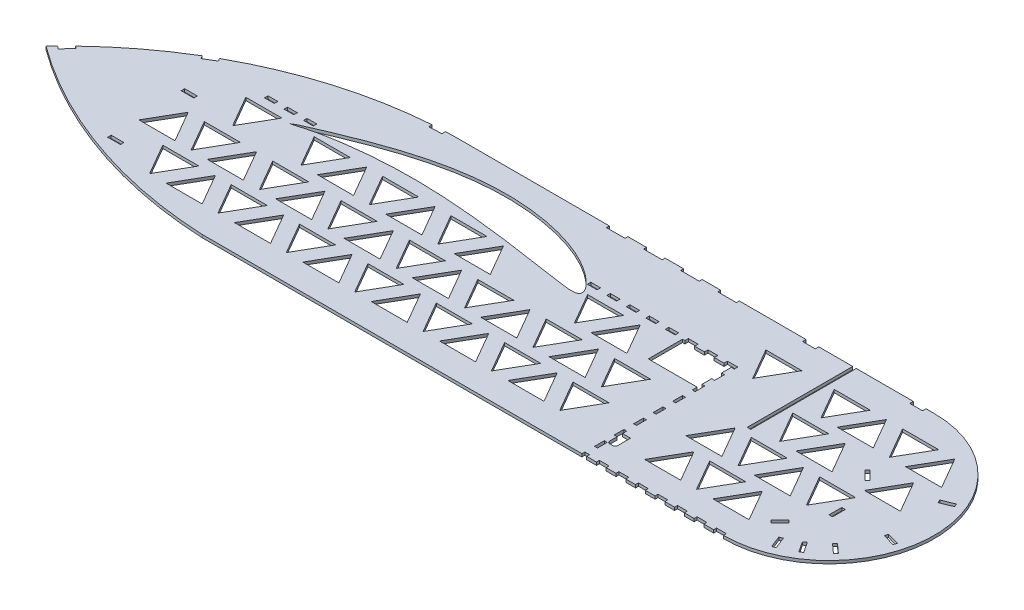
SolidWorks part; units mm, degrees
ref_plane "Front Plane" through (0, 0, 0) normal (0, 0, 1) x (1, 0, 0)
ref_plane "Top Plane" through (0, 0, 0) normal (0, 1, 0) x (1, 0, 0)
ref_plane "Right Plane" through (0, 0, 0) normal (1, 0, 0) x (0, 0, -1)
sketch "Sketch1" plane through (0, 0, 0) normal (0, 1, 0) x (1, 0, 0)
  line L0 (800, 108) -> (0, 108) construction
  line L1 (266.4083, 0) -> (800, 0)
  line L2 (0, 0) -> (0, 216) construction
  line L3 (316.2946, 216) -> (800, 216)
  arc A0 (800, 216) -> (800, 0) centre (800, 108) cw
  arc A2 (266.4083, 0) -> (19.4291, 86.8932) centre (286.1808, 450.645) cw
  arc A4 (19.4291, 86.8932) -> (316.2946, 216) centre (316.2946, -189.8565) cw
  dimension "D1" = 800
  dimension "D2" = 216
extrude "Boss-Extrude1" add sketch "Sketch1" along normal blind 3
sketch "Sketch2" plane through (0, 0, 0) normal (0, -1, 0) x (1, 0, 0)
  line L0 (605.07, -153) -> (605.07, 81) construction
  line L1 (647.57, -153) -> (637.57, -153)
  line L2 (655.07, -153) -> (655.07, -143)
  line L3 (655.07, -118) -> (605.07, -118)
  line L4 (823.6893, -121.2328) -> (814.4969, -130.4252)
  line L5 (814.4969, -130.4252) -> (817.0425, -132.9707)
  line L6 (817.0425, -132.9707) -> (826.2349, -123.7784)
  line L7 (826.2349, -123.7784) -> (823.6893, -121.2328)
  line L8 (823.6893, -121.2328) -> (814.4969, -130.4252)
  line L9 (814.4969, -130.4252) -> (817.0425, -132.9707)
  line L10 (817.0425, -132.9707) -> (826.2349, -123.7784)
  line L11 (826.2349, -123.7784) -> (823.6893, -121.2328)
  line L12 (605.07, -153) -> (605.07, -118)
  line L13 (778.5, -216) -> (791.5, -216) construction
  line L14 (791.5, -216) -> (791.5, -212.4) construction
  line L15 (791.5, -212.4) -> (778.5, -212.4) construction
  line L16 (778.5, -212.4) -> (778.5, -216) construction
  line L17 (668.6076, -216) -> (681.6076, -216) construction
  line L18 (681.6076, -216) -> (681.6076, -212.4) construction
  line L19 (681.6076, -212.4) -> (668.6076, -212.4) construction
  line L20 (833.2163, -28.1278) -> (837.9573, -16.0231)
  line L21 (837.9573, -16.0231) -> (834.6052, -14.7102)
  line L22 (834.6052, -14.7102) -> (829.8642, -26.8149)
  line L23 (829.8642, -26.8149) -> (833.2163, -28.1278)
  line L24 (833.2163, -28.1278) -> (837.9573, -16.0231)
  line L25 (837.9573, -16.0231) -> (834.6052, -14.7102)
  line L26 (834.6052, -14.7102) -> (829.8642, -26.8149)
  line L27 (829.8642, -26.8149) -> (833.2163, -28.1278)
  line L28 (839.4566, -85.3169) -> (839.4566, -72.3169)
  line L29 (839.4566, -72.3169) -> (835.8566, -72.3169)
  line L30 (835.8566, -72.3169) -> (835.8566, -85.3169)
  line L31 (835.8566, -85.3169) -> (839.4566, -85.3169)
  line L32 (839.4566, -85.3169) -> (839.4566, -72.3169)
  line L33 (839.4566, -72.3169) -> (835.8566, -72.3169)
  line L34 (835.8566, -72.3169) -> (835.8566, -85.3169)
  line L35 (835.8566, -85.3169) -> (839.4566, -85.3169)
  line L36 (668.6076, -212.4) -> (668.6076, -216) construction
  line L39 (600.2018, -213) -> (581.2018, -213) construction
  line L40 (658.07, -25.4734) -> (658.07, -38.6734)
  line L41 (663.77, -22.9734) -> (660.57, -22.9734)
  line L42 (666.27, -38.6734) -> (666.27, -25.4734)
  line L43 (658.07, -38.6734) -> (666.27, -38.6734)
  line L44 (658.07, -25.4734) -> (658.07, -33)
  line L45 (663.77, -22.9734) -> (660.57, -22.9734)
  line L46 (666.27, -38.6734) -> (666.27, -25.4734)
  line L47 (658.07, -38.6734) -> (666.27, -38.6734)
  line L48 (581.2018, -213) -> (581.2018, -216) construction
  line L49 (581.2018, -216) -> (600.2018, -216) construction
  line L50 (600.2018, -216) -> (600.2018, -213) construction
  line L51 (562.2018, -213) -> (543.2018, -213) construction
  line L52 (543.2018, -213) -> (543.2018, -216) construction
  line L53 (543.2018, -216) -> (562.2018, -216) construction
  line L54 (562.2018, -216) -> (562.2018, -213) construction
  line L55 (524.2018, -213) -> (505.2018, -213) construction
  line L56 (505.2018, -213) -> (505.2018, -216) construction
  line L57 (505.2018, -216) -> (524.2018, -216) construction
  line L58 (524.2018, -216) -> (524.2018, -213) construction
  line L59 (486.2018, -213) -> (467.2018, -213) construction
  line L60 (467.2018, -213) -> (467.2018, -216) construction
  line L61 (467.2018, -216) -> (486.2018, -216) construction
  line L62 (486.2018, -216) -> (486.2018, -213) construction
  line L63 (286.6536, -215.0679) -> (299.64, -215.6627) construction
  line L64 (299.64, -215.6627) -> (299.8047, -212.0664) construction
  line L65 (299.8047, -212.0664) -> (286.8183, -211.4717) construction
  line L66 (286.8183, -211.4717) -> (286.6536, -215.0679) construction
  line L67 (107.8918, -158.4076) -> (119.0512, -165.0761) construction
  line L68 (119.0512, -165.0761) -> (120.8979, -161.9858) construction
  line L69 (120.8979, -161.9858) -> (109.7385, -155.3173) construction
  line L70 (109.7385, -155.3173) -> (107.8918, -158.4076) construction
  line L71 (25.2251, -93.1105) -> (34.0897, -102.6194) construction
  line L72 (34.0897, -102.6194) -> (36.7229, -100.1646) construction
  line L73 (36.7229, -100.1646) -> (27.8584, -90.6557) construction
  line L74 (27.8584, -90.6557) -> (25.2251, -93.1105) construction
  line L76 (141.0425, -116.6591) -> (128.0425, -116.6591) construction
  line L77 (128.0425, -116.6591) -> (128.0425, -120.2591) construction
  line L79 (212.57, -142.8618) -> (212.57, -142.8948)
  line L80 (128.0425, -120.2591) -> (141.0425, -120.2591) construction
  line L81 (141.0425, -120.2591) -> (141.0425, -116.6591) construction
  line L82 (144.694, -37.8042) -> (131.694, -37.8042) construction
  line L83 (131.694, -37.8042) -> (131.694, -41.4042) construction
  line L84 (131.694, -41.4042) -> (144.694, -41.4042) construction
  line L85 (144.694, -41.4042) -> (144.694, -37.8042) construction
  line L99 (141.0425, -116.6591) -> (128.0425, -116.6591)
  line L101 (128.0425, -116.6591) -> (128.0425, -120.2591)
  line L102 (128.0425, -120.2591) -> (141.0425, -120.2591)
  line L104 (141.0425, -120.2591) -> (141.0425, -116.6591)
  line L105 (144.694, -37.8042) -> (131.694, -37.8042)
  line L106 (131.694, -37.8042) -> (131.694, -41.4042)
  line L108 (131.694, -41.4042) -> (144.694, -41.4042)
  line L110 (144.694, -41.4042) -> (144.694, -37.8042)
  line L111 (237.2859, -101.1604) -> (274.2268, -101.1604)
  line L131 (537.57, -153) -> (527.57, -153) construction
  line L132 (527.57, -153) -> (527.57, -156.6) construction
  line L133 (527.57, -156.6) -> (537.57, -156.6) construction
  line L134 (537.57, -156.6) -> (537.57, -153) construction
  line L135 (557.57, -153) -> (547.57, -153) construction
  line L136 (547.57, -153) -> (547.57, -156.6) construction
  line L137 (547.57, -156.6) -> (557.57, -156.6) construction
  line L138 (557.57, -156.6) -> (557.57, -153) construction
  line L139 (577.57, -153) -> (567.57, -153) construction
  line L140 (567.57, -153) -> (567.57, -156.6) construction
  line L141 (567.57, -156.6) -> (577.57, -156.6) construction
  line L142 (577.57, -156.6) -> (577.57, -153) construction
  line L143 (597.57, -153) -> (587.57, -153) construction
  line L144 (587.57, -153) -> (587.57, -156.6) construction
  line L145 (587.57, -156.6) -> (597.57, -156.6) construction
  line L146 (597.57, -156.6) -> (597.57, -153) construction
  line L148 (607.57, -153) -> (607.57, -156.6) construction
  line L149 (607.57, -156.6) -> (617.57, -156.6) construction
  line L150 (617.57, -156.6) -> (617.57, -153) construction
  line L152 (627.57, -153) -> (627.57, -156.6) construction
  line L153 (627.57, -156.6) -> (637.57, -156.6) construction
  line L154 (637.57, -156.6) -> (637.57, -153) construction
  line L155 (658.07, -153) -> (647.57, -153) construction
  line L156 (647.57, -153) -> (647.57, -156.6) construction
  line L157 (647.57, -156.6) -> (658.07, -156.6) construction
  line L158 (658.07, -156.6) -> (658.07, -153) construction
  line L160 (655.07, -143) -> (658.07, -143) construction
  line L161 (658.07, -143) -> (658.07, -133) construction
  line L162 (658.07, -133) -> (655.07, -133) construction
  line L163 (655.07, -113) -> (655.07, -123) construction
  line L164 (655.07, -123) -> (658.07, -123) construction
  line L165 (658.07, -123) -> (658.07, -113) construction
  line L166 (658.07, -113) -> (655.07, -113) construction
  line L167 (655.07, -93) -> (655.07, -103) construction
  line L168 (655.07, -103) -> (658.07, -103) construction
  line L169 (658.07, -103) -> (658.07, -93) construction
  line L170 (658.07, -93) -> (655.07, -93) construction
  line L171 (655.07, -73) -> (655.07, -83) construction
  line L172 (655.07, -83) -> (658.07, -83) construction
  line L173 (658.07, -83) -> (658.07, -73) construction
  line L174 (658.07, -73) -> (655.07, -73) construction
  line L175 (655.07, -53) -> (655.07, -63) construction
  line L176 (655.07, -63) -> (658.07, -63) construction
  line L177 (658.07, -63) -> (658.07, -53) construction
  line L178 (658.07, -53) -> (655.07, -53) construction
  line L179 (655.07, -33) -> (655.07, -43) construction
  line L180 (655.07, -43) -> (658.07, -43) construction
  line L182 (658.07, -33) -> (655.07, -33) construction
  line L183 (655.07, -13) -> (655.07, -23) construction
  line L184 (655.07, -23) -> (658.07, -23) construction
  line L185 (658.07, -23) -> (658.07, -13) construction
  line L186 (658.07, -13) -> (655.07, -13) construction
  line L187 (660, 0) -> (655.07, 0) construction
  line L188 (879.4661, -142.1765) -> (891.5128, -147.063) construction
  line L189 (891.5128, -147.063) -> (892.866, -143.727) construction
  line L190 (892.866, -143.727) -> (880.8193, -138.8405) construction
  line L191 (880.8193, -138.8405) -> (879.4661, -142.1765) construction
  line L192 (883.5641, -85.6407) -> (896.0497, -82.0199) construction
  line L193 (896.0497, -82.0199) -> (895.047, -78.5624) construction
  line L194 (895.047, -78.5624) -> (882.5614, -82.1832) construction
  line L195 (882.5614, -82.1832) -> (883.5641, -85.6407) construction
  line L196 (865.4007, -51.3816) -> (875.0501, -42.6702) construction
  line L197 (875.0501, -42.6702) -> (872.6378, -39.9981) construction
  line L198 (872.6378, -39.9981) -> (862.9883, -48.7095) construction
  line L199 (862.9883, -48.7095) -> (865.4007, -51.3816) construction
  line L200 (849.1147, -36.7915) -> (856.2715, -25.9389) construction
  line L201 (856.2715, -25.9389) -> (853.2661, -23.957) construction
  line L202 (853.2661, -23.957) -> (846.1093, -34.8096) construction
  line L203 (846.1093, -34.8096) -> (849.1147, -36.7915) construction
  line L204 (822.4089, -44.7346) -> (813.2165, -35.5422) construction
  line L205 (813.2165, -35.5422) -> (810.6709, -38.0878) construction
  line L206 (810.6709, -38.0878) -> (819.8633, -47.2801) construction
  line L207 (819.8633, -47.2801) -> (822.4089, -44.7346) construction
  line L208 (879.4661, -142.1765) -> (891.5128, -147.063)
  line L209 (891.5128, -147.063) -> (892.866, -143.727)
  line L210 (892.866, -143.727) -> (880.8193, -138.8405)
  line L211 (880.8193, -138.8405) -> (879.4661, -142.1765)
  line L212 (883.5641, -85.6407) -> (896.0497, -82.0199)
  line L213 (896.0497, -82.0199) -> (895.047, -78.5624)
  line L214 (895.047, -78.5624) -> (882.5614, -82.1832)
  line L215 (882.5614, -82.1832) -> (883.5641, -85.6407)
  line L216 (865.4007, -51.3816) -> (875.0501, -42.6702)
  line L217 (875.0501, -42.6702) -> (872.6378, -39.9981)
  line L218 (872.6378, -39.9981) -> (862.9883, -48.7095)
  line L219 (862.9883, -48.7095) -> (865.4007, -51.3816)
  line L220 (849.1147, -36.7915) -> (856.2715, -25.9389)
  line L221 (856.2715, -25.9389) -> (853.2661, -23.957)
  line L222 (853.2661, -23.957) -> (846.1093, -34.8096)
  line L223 (846.1093, -34.8096) -> (849.1147, -36.7915)
  line L224 (822.4089, -44.7346) -> (813.2165, -35.5422)
  line L225 (813.2165, -35.5422) -> (810.6709, -38.0878)
  line L226 (810.6709, -38.0878) -> (819.8633, -47.2801)
  line L227 (819.8633, -47.2801) -> (822.4089, -44.7346)
  line L228 (655.07, 0) -> (655.07, -3) construction
  line L229 (655.07, -3) -> (660, -3) construction
  line L230 (660, -3) -> (660, 0) construction
  line L231 (680, 0) -> (670, 0) construction
  line L232 (670, 0) -> (670, -3) construction
  line L233 (670, -3) -> (680, -3) construction
  line L234 (680, -3) -> (680, 0) construction
  line L235 (700, 0) -> (690, 0) construction
  line L236 (690, 0) -> (690, -3) construction
  line L237 (690, -3) -> (700, -3) construction
  line L238 (700, -3) -> (700, 0) construction
  line L239 (720, 0) -> (710, 0) construction
  line L240 (710, 0) -> (710, -3) construction
  line L241 (710, -3) -> (720, -3) construction
  line L242 (720, -3) -> (720, 0) construction
  line L243 (740, 0) -> (730, 0) construction
  line L244 (730, 0) -> (730, -3) construction
  line L245 (730, -3) -> (740, -3) construction
  line L246 (740, -3) -> (740, 0) construction
  line L247 (760, 0) -> (750, 0) construction
  line L248 (750, 0) -> (750, -3) construction
  line L249 (750, -3) -> (760, -3) construction
  line L250 (760, -3) -> (760, 0) construction
  line L251 (780, 0) -> (770, 0) construction
  line L252 (770, 0) -> (770, -3) construction
  line L253 (770, -3) -> (780, -3) construction
  line L254 (780, -3) -> (780, 0) construction
  line L255 (800, 0) -> (790, 0) construction
  line L256 (790, 0) -> (790, -3) construction
  line L257 (790, -3) -> (800, -3) construction
  line L258 (800, -3) -> (800, 0) construction
  line L259 (778.5, -216) -> (791.5, -216)
  line L260 (791.5, -216) -> (791.5, -212.4)
  line L261 (791.5, -212.4) -> (778.5, -212.4)
  line L262 (778.5, -212.4) -> (778.5, -216)
  line L263 (668.6076, -216) -> (681.6076, -216)
  line L264 (681.6076, -216) -> (681.6076, -212.4)
  line L265 (681.6076, -212.4) -> (668.6076, -212.4)
  line L266 (668.6076, -212.4) -> (668.6076, -216)
  line L267 (600.2018, -213) -> (581.2018, -213)
  line L268 (581.2018, -213) -> (581.2018, -216)
  line L269 (581.2018, -216) -> (600.2018, -216)
  line L270 (600.2018, -216) -> (600.2018, -213)
  line L271 (562.2018, -213) -> (543.2018, -213)
  line L272 (543.2018, -213) -> (543.2018, -216)
  line L273 (543.2018, -216) -> (562.2018, -216)
  line L274 (562.2018, -216) -> (562.2018, -213)
  line L275 (524.2018, -213) -> (505.2018, -213)
  line L276 (505.2018, -213) -> (505.2018, -216)
  line L277 (505.2018, -216) -> (524.2018, -216)
  line L278 (524.2018, -216) -> (524.2018, -213)
  line L279 (486.2018, -213) -> (467.2018, -213)
  line L280 (467.2018, -213) -> (467.2018, -216)
  line L281 (467.2018, -216) -> (486.2018, -216)
  line L282 (486.2018, -216) -> (486.2018, -213)
  line L283 (286.6536, -215.0679) -> (299.64, -215.6627)
  line L284 (299.64, -215.6627) -> (299.8047, -212.0664)
  line L285 (299.8047, -212.0664) -> (286.8183, -211.4717)
  line L286 (286.8183, -211.4717) -> (286.6536, -215.0679)
  line L287 (107.8918, -158.4076) -> (119.0512, -165.0761)
  line L288 (119.0512, -165.0761) -> (120.8979, -161.9858)
  line L289 (120.8979, -161.9858) -> (109.7385, -155.3173)
  line L290 (109.7385, -155.3173) -> (107.8918, -158.4076)
  line L291 (25.2251, -93.1105) -> (34.0897, -102.6194)
  line L292 (34.0897, -102.6194) -> (36.7229, -100.1646)
  line L293 (36.7229, -100.1646) -> (27.8584, -90.6557)
  line L294 (27.8584, -90.6557) -> (25.2251, -93.1105)
  line L351 (537.57, -153) -> (527.57, -153)
  line L352 (527.57, -153) -> (527.57, -156.6)
  line L353 (527.57, -156.6) -> (537.57, -156.6)
  line L354 (537.57, -156.6) -> (537.57, -153)
  line L355 (557.57, -153) -> (547.57, -153)
  line L356 (547.57, -153) -> (547.57, -156.6)
  line L357 (547.57, -156.6) -> (557.57, -156.6)
  line L358 (557.57, -156.6) -> (557.57, -153)
  line L359 (577.57, -153) -> (567.57, -153)
  line L360 (567.57, -153) -> (567.57, -156.6)
  line L361 (567.57, -156.6) -> (577.57, -156.6)
  line L362 (577.57, -156.6) -> (577.57, -153)
  line L363 (597.57, -153) -> (587.57, -153)
  line L364 (587.57, -153) -> (587.57, -156.6)
  line L365 (587.57, -156.6) -> (597.57, -156.6)
  line L366 (597.57, -156.6) -> (597.57, -153)
  line L368 (607.57, -153) -> (607.57, -156.6)
  line L369 (607.57, -156.6) -> (617.57, -156.6)
  line L370 (617.57, -156.6) -> (617.57, -153)
  line L372 (627.57, -153) -> (627.57, -156.6)
  line L373 (627.57, -156.6) -> (637.57, -156.6)
  line L374 (637.57, -156.6) -> (637.57, -153)
  line L375 (658.07, -153) -> (655.07, -153)
  line L376 (647.57, -153) -> (647.57, -156.6)
  line L377 (647.57, -156.6) -> (658.07, -156.6)
  line L378 (658.07, -156.6) -> (658.07, -153)
  line L380 (655.07, -143) -> (658.07, -143)
  line L381 (658.07, -143) -> (658.07, -133)
  line L382 (658.07, -133) -> (655.07, -133)
  line L383 (655.07, -113) -> (655.07, -118)
  line L384 (655.07, -123) -> (658.07, -123)
  line L385 (658.07, -123) -> (658.07, -113)
  line L386 (658.07, -113) -> (655.07, -113)
  line L387 (655.07, -93) -> (655.07, -103)
  line L388 (655.07, -103) -> (658.07, -103)
  line L389 (658.07, -103) -> (658.07, -93)
  line L390 (658.07, -93) -> (655.07, -93)
  line L391 (655.07, -73) -> (655.07, -83)
  line L392 (655.07, -83) -> (658.07, -83)
  line L393 (658.07, -83) -> (658.07, -73)
  line L394 (658.07, -73) -> (655.07, -73)
  line L395 (655.07, -53) -> (655.07, -63)
  line L396 (655.07, -63) -> (658.07, -63)
  line L397 (658.07, -63) -> (658.07, -53)
  line L398 (658.07, -53) -> (655.07, -53)
  line L399 (655.07, -33) -> (655.07, -43)
  line L400 (655.07, -43) -> (658.07, -43)
  line L401 (658.07, -43) -> (658.07, -38.6734)
  line L402 (658.07, -33) -> (655.07, -33)
  line L403 (655.07, -13) -> (655.07, -23)
  line L404 (655.07, -23) -> (658.07, -23)
  line L405 (658.07, -23) -> (658.07, -13)
  line L406 (658.07, -13) -> (655.07, -13)
  line L407 (660, 0) -> (655.07, 0)
  line L408 (655.07, 0) -> (655.07, -3)
  line L409 (655.07, -3) -> (660, -3)
  line L410 (660, -3) -> (660, 0)
  line L411 (680, 0) -> (670, 0)
  line L412 (670, 0) -> (670, -3)
  line L413 (670, -3) -> (680, -3)
  line L414 (680, -3) -> (680, 0)
  line L415 (700, 0) -> (690, 0)
  line L416 (690, 0) -> (690, -3)
  line L417 (690, -3) -> (700, -3)
  line L418 (700, -3) -> (700, 0)
  line L419 (720, 0) -> (710, 0)
  line L420 (710, 0) -> (710, -3)
  line L421 (710, -3) -> (720, -3)
  line L422 (720, -3) -> (720, 0)
  line L423 (740, 0) -> (730, 0)
  line L424 (730, 0) -> (730, -3)
  line L425 (730, -3) -> (740, -3)
  line L426 (740, -3) -> (740, 0)
  line L427 (760, 0) -> (750, 0)
  line L428 (750, 0) -> (750, -3)
  line L429 (750, -3) -> (760, -3)
  line L430 (760, -3) -> (760, 0)
  line L431 (780, 0) -> (770, 0)
  line L432 (770, 0) -> (770, -3)
  line L433 (770, -3) -> (780, -3)
  line L434 (780, -3) -> (780, 0)
  line L435 (800, 0) -> (790, 0)
  line L436 (790, 0) -> (790, -3)
  line L437 (790, -3) -> (800, -3)
  line L438 (800, -3) -> (800, 0)
  line L439 (655.07, -133) -> (655.07, -123)
  line L440 (627.57, -153) -> (617.57, -153)
  line L441 (607.57, -153) -> (605.07, -153)
  line L443 (274.2268, -101.1604) -> (255.7563, -69.1686)
  line L444 (255.7563, -69.1686) -> (237.2859, -101.1604)
  line L445 (202.2859, -69.1686) -> (239.2268, -69.1686)
  line L449 (239.2268, -69.1686) -> (220.7563, -101.1604)
  line L450 (220.7563, -101.1604) -> (202.2859, -69.1686)
  line L451 (220.7563, -101.1604) -> (202.2859, -69.1686) construction
  line L452 (239.2268, -69.1686) -> (220.7563, -101.1604) construction
  line L453 (202.2859, -69.1686) -> (239.2268, -69.1686) construction
  line L462 (187.07, -153) -> (177.07, -153) construction
  line L463 (177.07, -153) -> (177.07, -156.6) construction
  line L464 (177.07, -156.6) -> (187.07, -156.6) construction
  line L465 (187.07, -156.6) -> (187.07, -153) construction
  line L466 (207.07, -153) -> (197.07, -153) construction
  line L467 (197.07, -153) -> (197.07, -156.6) construction
  line L468 (197.07, -156.6) -> (207.07, -156.6) construction
  line L469 (207.07, -156.6) -> (207.07, -153) construction
  line L470 (227.07, -153) -> (217.07, -153) construction
  line L471 (217.07, -153) -> (217.07, -156.6) construction
  line L472 (217.07, -156.6) -> (227.07, -156.6) construction
  line L473 (227.07, -156.6) -> (227.07, -153) construction
  line L474 (517.57, -153) -> (507.57, -153) construction
  line L475 (507.57, -153) -> (507.57, -156.6) construction
  line L476 (507.57, -156.6) -> (517.57, -156.6) construction
  line L477 (517.57, -156.6) -> (517.57, -153) construction
  line L478 (187.07, -153) -> (177.07, -153)
  line L479 (177.07, -153) -> (177.07, -156.6)
  line L480 (177.07, -156.6) -> (187.07, -156.6)
  line L481 (187.07, -156.6) -> (187.07, -153)
  line L482 (207.07, -153) -> (197.07, -153)
  line L483 (197.07, -153) -> (197.07, -156.6)
  line L484 (197.07, -156.6) -> (207.07, -156.6)
  line L485 (207.07, -156.6) -> (207.07, -153)
  line L486 (227.07, -153) -> (217.07, -153)
  line L487 (217.07, -153) -> (217.07, -156.6)
  line L488 (217.07, -156.6) -> (227.07, -156.6)
  line L489 (227.07, -156.6) -> (227.07, -153)
  line L490 (517.57, -153) -> (507.57, -153)
  line L491 (507.57, -153) -> (507.57, -156.6)
  line L492 (507.57, -156.6) -> (517.57, -156.6)
  line L493 (517.57, -156.6) -> (517.57, -153)
  line L504 (202.2859, -26.9901) -> (239.2268, -26.9901)
  line L514 (239.2268, -26.9901) -> (220.7563, -58.9818)
  line L515 (132.2859, -69.1686) -> (169.2268, -69.1686)
  line L516 (150.7563, -101.1604) -> (132.2859, -69.1686)
  line L517 (169.2268, -69.1686) -> (150.7563, -101.1604)
  line L518 (202.2859, -69.1686) -> (132.2859, -69.1686) construction
  line L519 (150.7563, -101.1604) -> (220.7563, -101.1604) construction
  line L520 (221.2596, -58.9818) -> (202.7892, -26.9901) construction
  line L521 (167.2859, -101.1604) -> (204.2268, -101.1604)
  line L522 (185.7563, -69.1686) -> (167.2859, -101.1604)
  line L523 (204.2268, -101.1604) -> (185.7563, -69.1686)
  line L524 (239.73, -26.9901) -> (221.2596, -58.9818) construction
  line L525 (202.7892, -26.9901) -> (239.73, -26.9901) construction
  line L526 (132.2859, -26.9901) -> (169.2268, -26.9901) construction
  line L527 (150.7563, -58.9818) -> (132.2859, -26.9901) construction
  line L528 (169.2268, -26.9901) -> (150.7563, -58.9818) construction
  line L529 (166.9552, -58.9818) -> (203.896, -58.9818)
  line L530 (185.4256, -26.9901) -> (166.9552, -58.9818)
  line L531 (203.896, -58.9818) -> (185.4256, -26.9901)
  line L532 (220.7563, -58.9818) -> (202.2859, -26.9901)
  line L533 (236.9552, -58.9818) -> (273.896, -58.9818)
  line L534 (716.4, -108) -> (716.4, -216)
  line L535 (716.4, -216) -> (720, -216)
  line L536 (720, -216) -> (720, -108)
  line L537 (720, -108) -> (716.4, -108)
  line L538 (716.4, -108) -> (716.4, -216)
  line L539 (716.4, -216) -> (720, -216)
  line L540 (720, -216) -> (720, -108)
  line L541 (720, -108) -> (716.4, -108)
  line L542 (273.896, -58.9818) -> (255.4256, -26.9901)
  line L543 (255.4256, -26.9901) -> (236.9552, -58.9818)
  line L544 (307.2859, -101.1604) -> (344.2268, -101.1604)
  line L545 (344.2268, -101.1604) -> (325.7563, -69.1686)
  line L546 (325.7563, -69.1686) -> (307.2859, -101.1604)
  line L547 (272.2859, -69.1686) -> (309.2268, -69.1686)
  line L548 (309.2268, -69.1686) -> (290.7563, -101.1604)
  line L549 (290.7563, -101.1604) -> (272.2859, -69.1686)
  line L550 (272.2859, -26.9901) -> (309.2268, -26.9901)
  line L551 (309.2268, -26.9901) -> (290.7563, -58.9818)
  line L552 (290.7563, -58.9818) -> (272.2859, -26.9901)
  line L553 (306.9552, -58.9818) -> (343.896, -58.9818)
  line L554 (343.896, -58.9818) -> (325.4256, -26.9901)
  line L555 (325.4256, -26.9901) -> (306.9552, -58.9818)
  line L556 (377.2859, -101.1604) -> (414.2268, -101.1604)
  line L557 (414.2268, -101.1604) -> (395.7563, -69.1686)
  line L558 (395.7563, -69.1686) -> (377.2859, -101.1604)
  line L559 (342.2859, -69.1686) -> (379.2268, -69.1686)
  line L560 (379.2268, -69.1686) -> (360.7563, -101.1604)
  line L561 (360.7563, -101.1604) -> (342.2859, -69.1686)
  line L562 (342.2859, -26.9901) -> (379.2268, -26.9901)
  line L563 (379.2268, -26.9901) -> (360.7563, -58.9818)
  line L564 (360.7563, -58.9818) -> (342.2859, -26.9901)
  line L565 (376.9552, -58.9818) -> (413.896, -58.9818)
  line L566 (413.896, -58.9818) -> (395.4256, -26.9901)
  line L567 (395.4256, -26.9901) -> (376.9552, -58.9818)
  line L568 (447.2859, -101.1604) -> (484.2268, -101.1604)
  line L569 (484.2268, -101.1604) -> (465.7563, -69.1686)
  line L570 (465.7563, -69.1686) -> (447.2859, -101.1604)
  line L571 (412.2859, -69.1686) -> (449.2268, -69.1686)
  line L572 (449.2268, -69.1686) -> (430.7563, -101.1604)
  line L573 (430.7563, -101.1604) -> (412.2859, -69.1686)
  line L574 (412.2859, -26.9901) -> (449.2268, -26.9901)
  line L575 (449.2268, -26.9901) -> (430.7563, -58.9818)
  line L576 (430.7563, -58.9818) -> (412.2859, -26.9901)
  line L577 (446.9552, -58.9818) -> (483.896, -58.9818)
  line L578 (483.896, -58.9818) -> (465.4256, -26.9901)
  line L579 (465.4256, -26.9901) -> (446.9552, -58.9818)
  line L580 (517.2859, -101.1604) -> (554.2268, -101.1604)
  line L581 (554.2268, -101.1604) -> (535.7563, -69.1686)
  line L582 (535.7563, -69.1686) -> (517.2859, -101.1604)
  line L583 (482.2859, -69.1686) -> (519.2268, -69.1686)
  line L584 (519.2268, -69.1686) -> (500.7563, -101.1604)
  line L585 (500.7563, -101.1604) -> (482.2859, -69.1686)
  line L586 (482.2859, -26.9901) -> (519.2268, -26.9901)
  line L587 (519.2268, -26.9901) -> (500.7563, -58.9818)
  line L588 (500.7563, -58.9818) -> (482.2859, -26.9901)
  line L589 (516.9552, -58.9818) -> (553.896, -58.9818)
  line L590 (553.896, -58.9818) -> (535.4256, -26.9901)
  line L591 (535.4256, -26.9901) -> (516.9552, -58.9818)
  line L592 (587.2859, -101.1604) -> (624.2268, -101.1604)
  line L593 (624.2268, -101.1604) -> (605.7563, -69.1686)
  line L594 (605.7563, -69.1686) -> (587.2859, -101.1604)
  line L595 (552.2859, -69.1686) -> (589.2268, -69.1686)
  line L596 (589.2268, -69.1686) -> (570.7563, -101.1604)
  line L597 (570.7563, -101.1604) -> (552.2859, -69.1686)
  line L598 (552.2859, -26.9901) -> (589.2268, -26.9901)
  line L599 (589.2268, -26.9901) -> (570.7563, -58.9818)
  line L600 (570.7563, -58.9818) -> (552.2859, -26.9901)
  line L601 (586.9552, -58.9818) -> (623.896, -58.9818)
  line L602 (623.896, -58.9818) -> (605.4256, -26.9901)
  line L603 (605.4256, -26.9901) -> (586.9552, -58.9818)
  line L616 (727.2859, -101.1604) -> (764.2268, -101.1604)
  line L617 (764.2268, -101.1604) -> (745.7563, -69.1686)
  line L618 (745.7563, -69.1686) -> (727.2859, -101.1604)
  line L619 (692.2859, -69.1686) -> (729.2268, -69.1686)
  line L620 (729.2268, -69.1686) -> (710.7563, -101.1604)
  line L621 (710.7563, -101.1604) -> (692.2859, -69.1686)
  line L622 (692.2859, -26.9901) -> (729.2268, -26.9901)
  line L623 (729.2268, -26.9901) -> (710.7563, -58.9818)
  line L624 (710.7563, -58.9818) -> (692.2859, -26.9901)
  line L625 (726.9552, -58.9818) -> (763.896, -58.9818)
  line L626 (763.896, -58.9818) -> (745.4256, -26.9901)
  line L627 (745.4256, -26.9901) -> (726.9552, -58.9818)
  line L628 (797.2859, -101.1604) -> (834.2268, -101.1604)
  line L629 (834.2268, -101.1604) -> (815.7563, -69.1686)
  line L630 (815.7563, -69.1686) -> (797.2859, -101.1604)
  line L631 (762.2859, -69.1686) -> (799.2268, -69.1686)
  line L632 (799.2268, -69.1686) -> (780.7563, -101.1604)
  line L633 (780.7563, -101.1604) -> (762.2859, -69.1686)
  line L634 (762.2859, -26.9901) -> (799.2268, -26.9901)
  line L635 (799.2268, -26.9901) -> (780.7563, -58.9818)
  line L636 (780.7563, -58.9818) -> (762.2859, -26.9901)
  line L661 (236.9552, -143.9818) -> (273.896, -143.9818)
  line L662 (273.896, -143.9818) -> (255.4256, -111.9901)
  line L663 (255.4256, -111.9901) -> (236.9552, -143.9818)
  line L670 (272.2859, -111.9901) -> (309.2268, -111.9901)
  line L671 (309.2268, -111.9901) -> (290.7563, -143.9818)
  line L672 (290.7563, -143.9818) -> (272.2859, -111.9901)
  line L673 (306.9552, -143.9818) -> (343.896, -143.9818)
  line L674 (343.896, -143.9818) -> (325.4256, -111.9901)
  line L675 (325.4256, -111.9901) -> (306.9552, -143.9818)
  line L682 (342.2859, -111.9901) -> (379.2268, -111.9901)
  line L683 (379.2268, -111.9901) -> (360.7563, -143.9818)
  line L684 (360.7563, -143.9818) -> (342.2859, -111.9901)
  line L685 (376.9552, -143.9818) -> (413.896, -143.9818)
  line L686 (413.896, -143.9818) -> (395.4256, -111.9901)
  line L687 (395.4256, -111.9901) -> (376.9552, -143.9818)
  line L694 (412.2859, -111.9901) -> (449.2268, -111.9901)
  line L695 (449.2268, -111.9901) -> (430.7563, -143.9818)
  line L696 (430.7563, -143.9818) -> (412.2859, -111.9901)
  line L709 (516.9552, -143.9818) -> (553.896, -143.9818)
  line L710 (553.896, -143.9818) -> (535.4256, -111.9901)
  line L711 (535.4256, -111.9901) -> (516.9552, -143.9818)
  line L718 (552.2859, -111.9901) -> (589.2268, -111.9901)
  line L719 (589.2268, -111.9901) -> (570.7563, -143.9818)
  line L720 (570.7563, -143.9818) -> (552.2859, -111.9901)
  line L724 (657.2859, -186.1604) -> (694.2268, -186.1604)
  line L725 (694.2268, -186.1604) -> (675.7563, -154.1686)
  line L726 (675.7563, -154.1686) -> (657.2859, -186.1604)
  line L736 (727.2859, -186.1604) -> (764.2268, -186.1604)
  line L737 (764.2268, -186.1604) -> (745.7563, -154.1686)
  line L738 (745.7563, -154.1686) -> (727.2859, -186.1604)
  line L745 (726.9552, -143.9818) -> (763.896, -143.9818)
  line L746 (763.896, -143.9818) -> (745.4256, -111.9901)
  line L747 (745.4256, -111.9901) -> (726.9552, -143.9818)
  line L748 (797.2859, -186.1604) -> (834.2268, -186.1604)
  line L749 (834.2268, -186.1604) -> (815.7563, -154.1686)
  line L750 (815.7563, -154.1686) -> (797.2859, -186.1604)
  line L751 (762.2859, -154.1686) -> (799.2268, -154.1686)
  line L752 (799.2268, -154.1686) -> (780.7563, -186.1604)
  line L753 (780.7563, -186.1604) -> (762.2859, -154.1686)
  line L754 (762.2859, -111.9901) -> (799.2268, -111.9901)
  line L755 (799.2268, -111.9901) -> (780.7563, -143.9818)
  line L756 (780.7563, -143.9818) -> (762.2859, -111.9901)
  line L763 (832.2859, -154.1686) -> (869.2268, -154.1686)
  line L764 (869.2268, -154.1686) -> (850.7563, -186.1604)
  line L765 (850.7563, -186.1604) -> (832.2859, -154.1686)
  line L766 (832.2859, -111.9901) -> (869.2268, -111.9901)
  line L767 (869.2268, -111.9901) -> (850.7563, -143.9818)
  line L768 (850.7563, -143.9818) -> (832.2859, -111.9901)
  line L901 (166.9552, -143.9818) -> (203.896, -143.9818)
  line L902 (203.896, -143.9818) -> (185.4256, -111.9901)
  line L903 (185.4256, -111.9901) -> (166.9552, -143.9818)
  line L916 (167.2859, -101.1604) -> (237.2859, -101.1604) construction
  line L917 (167.2859, -101.1604) -> (167.2859, -186.1604) construction
  line L918 (832.2859, -69.1686) -> (869.2268, -69.1686) [skipped]
  line L919 (869.2268, -69.1686) -> (850.7563, -101.1604) [skipped]
  line L920 (850.7563, -101.1604) -> (832.2859, -69.1686) [skipped]
  line L921 (796.9552, -58.9818) -> (833.896, -58.9818) [skipped]
  line L922 (833.896, -58.9818) -> (815.4256, -26.9901) [skipped]
  line L923 (815.4256, -26.9901) -> (796.9552, -58.9818) [skipped]
  line L924 (796.9552, -143.9818) -> (833.896, -143.9818) [skipped]
  line L925 (833.896, -143.9818) -> (815.4256, -111.9901) [skipped]
  line L926 (815.4256, -111.9901) -> (796.9552, -143.9818) [skipped]
  line L927 (866.9552, -58.9818) -> (903.896, -58.9818) [skipped]
  line L928 (903.896, -58.9818) -> (885.4256, -26.9901) [skipped]
  line L929 (885.4256, -26.9901) -> (866.9552, -58.9818) [skipped]
  line L930 (832.2859, -26.9901) -> (869.2268, -26.9901) [skipped]
  line L931 (869.2268, -26.9901) -> (850.7563, -58.9818) [skipped]
  line L932 (850.7563, -58.9818) -> (832.2859, -26.9901) [skipped]
  line L933 (867.2859, -101.1604) -> (904.2268, -101.1604) [skipped]
  line L934 (904.2268, -101.1604) -> (885.7563, -69.1686) [skipped]
  line L935 (885.7563, -69.1686) -> (867.2859, -101.1604) [skipped]
  line L936 (866.9552, -143.9818) -> (903.896, -143.9818) [skipped]
  line L937 (903.896, -143.9818) -> (885.4256, -111.9901) [skipped]
  line L938 (885.4256, -111.9901) -> (866.9552, -143.9818) [skipped]
  line L939 (867.2859, -186.1604) -> (904.2268, -186.1604) [skipped]
  line L940 (904.2268, -186.1604) -> (885.7563, -154.1686) [skipped]
  line L941 (885.7563, -154.1686) -> (867.2859, -186.1604) [skipped]
  line L942 (832.2859, -196.9901) -> (869.2268, -196.9901) [skipped]
  line L943 (869.2268, -196.9901) -> (850.7563, -228.9818) [skipped]
  line L944 (850.7563, -228.9818) -> (832.2859, -196.9901) [skipped]
  line L945 (796.9552, -228.9818) -> (833.896, -228.9818) [skipped]
  line L946 (833.896, -228.9818) -> (815.4256, -196.9901) [skipped]
  line L947 (815.4256, -196.9901) -> (796.9552, -228.9818) [skipped]
  line L948 (866.9552, -228.9818) -> (903.896, -228.9818) [skipped]
  line L949 (903.896, -228.9818) -> (885.4256, -196.9901) [skipped]
  line L950 (885.4256, -196.9901) -> (866.9552, -228.9818) [skipped]
  line L951 (867.2859, -271.1604) -> (904.2268, -271.1604) [skipped]
  line L952 (904.2268, -271.1604) -> (885.7563, -239.1686) [skipped]
  line L953 (885.7563, -239.1686) -> (867.2859, -271.1604) [skipped]
  line L954 (832.2859, -239.1686) -> (869.2268, -239.1686) [skipped]
  line L955 (869.2268, -239.1686) -> (850.7563, -271.1604) [skipped]
  line L956 (850.7563, -271.1604) -> (832.2859, -239.1686) [skipped]
  line L957 (797.2859, -271.1604) -> (834.2268, -271.1604) [skipped]
  line L958 (834.2268, -271.1604) -> (815.7563, -239.1686) [skipped]
  line L959 (815.7563, -239.1686) -> (797.2859, -271.1604) [skipped]
  line L960 (762.2859, -239.1686) -> (799.2268, -239.1686) [skipped]
  line L961 (799.2268, -239.1686) -> (780.7563, -271.1604) [skipped]
  line L962 (780.7563, -271.1604) -> (762.2859, -239.1686) [skipped]
  line L963 (727.2859, -271.1604) -> (764.2268, -271.1604) [skipped]
  line L964 (764.2268, -271.1604) -> (745.7563, -239.1686) [skipped]
  line L965 (745.7563, -239.1686) -> (727.2859, -271.1604) [skipped]
  line L966 (692.2859, -239.1686) -> (729.2268, -239.1686) [skipped]
  line L967 (729.2268, -239.1686) -> (710.7563, -271.1604) [skipped]
  line L968 (710.7563, -271.1604) -> (692.2859, -239.1686) [skipped]
  line L969 (657.2859, -271.1604) -> (694.2268, -271.1604) [skipped]
  line L970 (694.2268, -271.1604) -> (675.7563, -239.1686) [skipped]
  line L971 (675.7563, -239.1686) -> (657.2859, -271.1604) [skipped]
  line L972 (622.2859, -239.1686) -> (659.2268, -239.1686) [skipped]
  line L973 (659.2268, -239.1686) -> (640.7563, -271.1604) [skipped]
  line L974 (640.7563, -271.1604) -> (622.2859, -239.1686) [skipped]
  line L975 (587.2859, -271.1604) -> (624.2268, -271.1604) [skipped]
  line L976 (624.2268, -271.1604) -> (605.7563, -239.1686) [skipped]
  line L977 (605.7563, -239.1686) -> (587.2859, -271.1604) [skipped]
  line L978 (552.2859, -239.1686) -> (589.2268, -239.1686) [skipped]
  line L979 (589.2268, -239.1686) -> (570.7563, -271.1604) [skipped]
  line L980 (570.7563, -271.1604) -> (552.2859, -239.1686) [skipped]
  line L981 (517.2859, -271.1604) -> (554.2268, -271.1604) [skipped]
  line L982 (554.2268, -271.1604) -> (535.7563, -239.1686) [skipped]
  line L983 (535.7563, -239.1686) -> (517.2859, -271.1604) [skipped]
  line L984 (482.2859, -239.1686) -> (519.2268, -239.1686) [skipped]
  line L985 (519.2268, -239.1686) -> (500.7563, -271.1604) [skipped]
  line L986 (500.7563, -271.1604) -> (482.2859, -239.1686) [skipped]
  line L987 (447.2859, -271.1604) -> (484.2268, -271.1604) [skipped]
  line L988 (484.2268, -271.1604) -> (465.7563, -239.1686) [skipped]
  line L989 (465.7563, -239.1686) -> (447.2859, -271.1604) [skipped]
  line L990 (762.2859, -196.9901) -> (799.2268, -196.9901) [skipped]
  line L991 (799.2268, -196.9901) -> (780.7563, -228.9818) [skipped]
  line L992 (780.7563, -228.9818) -> (762.2859, -196.9901) [skipped]
  line L993 (726.9552, -228.9818) -> (763.896, -228.9818) [skipped]
  line L994 (763.896, -228.9818) -> (745.4256, -196.9901) [skipped]
  line L995 (745.4256, -196.9901) -> (726.9552, -228.9818) [skipped]
  line L996 (692.2859, -196.9901) -> (729.2268, -196.9901) [skipped]
  line L997 (729.2268, -196.9901) -> (710.7563, -228.9818) [skipped]
  line L998 (710.7563, -228.9818) -> (692.2859, -196.9901) [skipped]
  line L999 (656.9552, -228.9818) -> (693.896, -228.9818) [skipped]
  line L1000 (693.896, -228.9818) -> (675.4256, -196.9901) [skipped]
  line L1001 (675.4256, -196.9901) -> (656.9552, -228.9818) [skipped]
  line L1002 (622.2859, -196.9901) -> (659.2268, -196.9901) [skipped]
  line L1003 (659.2268, -196.9901) -> (640.7563, -228.9818) [skipped]
  line L1004 (640.7563, -228.9818) -> (622.2859, -196.9901) [skipped]
  line L1005 (586.9552, -228.9818) -> (623.896, -228.9818) [skipped]
  line L1006 (623.896, -228.9818) -> (605.4256, -196.9901) [skipped]
  line L1007 (605.4256, -196.9901) -> (586.9552, -228.9818) [skipped]
  line L1008 (552.2859, -196.9901) -> (589.2268, -196.9901) [skipped]
  line L1009 (589.2268, -196.9901) -> (570.7563, -228.9818) [skipped]
  line L1010 (570.7563, -228.9818) -> (552.2859, -196.9901) [skipped]
  line L1011 (516.9552, -228.9818) -> (553.896, -228.9818) [skipped]
  line L1012 (553.896, -228.9818) -> (535.4256, -196.9901) [skipped]
  line L1013 (535.4256, -196.9901) -> (516.9552, -228.9818) [skipped]
  line L1014 (482.2859, -196.9901) -> (519.2268, -196.9901) [skipped]
  line L1015 (519.2268, -196.9901) -> (500.7563, -228.9818) [skipped]
  line L1016 (500.7563, -228.9818) -> (482.2859, -196.9901) [skipped]
  line L1017 (692.2859, -154.1686) -> (729.2268, -154.1686) [skipped]
  line L1018 (729.2268, -154.1686) -> (710.7563, -186.1604) [skipped]
  line L1019 (710.7563, -186.1604) -> (692.2859, -154.1686) [skipped]
  line L1020 (692.2859, -111.9901) -> (729.2268, -111.9901) [skipped]
  line L1021 (729.2268, -111.9901) -> (710.7563, -143.9818) [skipped]
  line L1022 (710.7563, -143.9818) -> (692.2859, -111.9901) [skipped]
  line L1023 (622.2859, -154.1686) -> (659.2268, -154.1686) [skipped]
  line L1024 (659.2268, -154.1686) -> (640.7563, -186.1604) [skipped]
  line L1025 (640.7563, -186.1604) -> (622.2859, -154.1686) [skipped]
  line L1026 (622.2859, -111.9901) -> (659.2268, -111.9901) [skipped]
  line L1027 (640.7563, -143.9818) -> (622.2859, -111.9901) [skipped]
  line L1028 (659.2268, -111.9901) -> (640.7563, -143.9818) [skipped]
  line L1029 (622.2859, -69.1686) -> (659.2268, -69.1686) [skipped]
  line L1030 (640.7563, -101.1604) -> (622.2859, -69.1686) [skipped]
  line L1031 (659.2268, -69.1686) -> (640.7563, -101.1604) [skipped]
  line L1032 (622.2859, -26.9901) -> (659.2268, -26.9901) [skipped]
  line L1033 (640.7563, -58.9818) -> (622.2859, -26.9901) [skipped]
  line L1034 (659.2268, -26.9901) -> (640.7563, -58.9818) [skipped]
  line L1035 (675.4256, -26.9901) -> (656.9552, -58.9818) [skipped]
  line L1036 (693.896, -58.9818) -> (675.4256, -26.9901) [skipped]
  line L1037 (656.9552, -58.9818) -> (693.896, -58.9818) [skipped]
  line L1038 (675.7563, -69.1686) -> (657.2859, -101.1604) [skipped]
  line L1039 (694.2268, -101.1604) -> (675.7563, -69.1686) [skipped]
  line L1040 (657.2859, -101.1604) -> (694.2268, -101.1604) [skipped]
  line L1041 (675.4256, -111.9901) -> (656.9552, -143.9818) [skipped]
  line L1042 (693.896, -143.9818) -> (675.4256, -111.9901) [skipped]
  line L1043 (656.9552, -143.9818) -> (693.896, -143.9818) [skipped]
  line L1044 (605.4256, -111.9901) -> (586.9552, -143.9818) [skipped]
  line L1045 (623.896, -143.9818) -> (605.4256, -111.9901) [skipped]
  line L1046 (586.9552, -143.9818) -> (623.896, -143.9818) [skipped]
  line L1047 (482.2859, -154.1686) -> (519.2268, -154.1686) [skipped]
  line L1048 (519.2268, -154.1686) -> (500.7563, -186.1604) [skipped]
  line L1049 (500.7563, -186.1604) -> (482.2859, -154.1686) [skipped]
  line L1050 (517.2859, -186.1604) -> (554.2268, -186.1604) [skipped]
  line L1051 (554.2268, -186.1604) -> (535.7563, -154.1686) [skipped]
  line L1052 (535.7563, -154.1686) -> (517.2859, -186.1604) [skipped]
  line L1053 (552.2859, -154.1686) -> (589.2268, -154.1686) [skipped]
  line L1054 (589.2268, -154.1686) -> (570.7563, -186.1604) [skipped]
  line L1055 (570.7563, -186.1604) -> (552.2859, -154.1686) [skipped]
  line L1056 (587.2859, -186.1604) -> (624.2268, -186.1604) [skipped]
  line L1057 (624.2268, -186.1604) -> (605.7563, -154.1686) [skipped]
  line L1058 (605.7563, -154.1686) -> (587.2859, -186.1604) [skipped]
  line L1059 (484.2268, -186.1604) -> (465.7563, -154.1686) [skipped]
  line L1060 (465.7563, -154.1686) -> (447.2859, -186.1604) [skipped]
  line L1061 (447.2859, -186.1604) -> (484.2268, -186.1604) [skipped]
  line L1062 (412.2859, -154.1686) -> (449.2268, -154.1686) [skipped]
  line L1063 (430.7563, -186.1604) -> (412.2859, -154.1686) [skipped]
  line L1064 (449.2268, -154.1686) -> (430.7563, -186.1604) [skipped]
  line L1065 (395.7563, -154.1686) -> (377.2859, -186.1604) [skipped]
  line L1066 (414.2268, -186.1604) -> (395.7563, -154.1686) [skipped]
  line L1067 (377.2859, -186.1604) -> (414.2268, -186.1604) [skipped]
  line L1068 (379.2268, -154.1686) -> (360.7563, -186.1604) [skipped]
  line L1069 (342.2859, -154.1686) -> (379.2268, -154.1686) [skipped]
  line L1070 (360.7563, -186.1604) -> (342.2859, -154.1686) [skipped]
  line L1071 (325.7563, -154.1686) -> (307.2859, -186.1604) [skipped]
  line L1072 (344.2268, -186.1604) -> (325.7563, -154.1686) [skipped]
  line L1073 (307.2859, -186.1604) -> (344.2268, -186.1604) [skipped]
  line L1074 (309.2268, -154.1686) -> (290.7563, -186.1604) [skipped]
  line L1075 (290.7563, -186.1604) -> (272.2859, -154.1686) [skipped]
  line L1076 (272.2859, -154.1686) -> (309.2268, -154.1686) [skipped]
  line L1077 (274.2268, -186.1604) -> (255.7563, -154.1686) [skipped]
  line L1078 (237.2859, -186.1604) -> (274.2268, -186.1604) [skipped]
  line L1079 (255.7563, -154.1686) -> (237.2859, -186.1604) [skipped]
  line L1080 (220.7563, -186.1604) -> (202.2859, -154.1686) [skipped]
  line L1081 (202.2859, -154.1686) -> (239.2268, -154.1686) [skipped]
  line L1082 (239.2268, -154.1686) -> (220.7563, -186.1604) [skipped]
  line L1083 (220.7563, -228.9818) -> (202.2859, -196.9901) [skipped]
  line L1084 (202.2859, -196.9901) -> (239.2268, -196.9901) [skipped]
  line L1085 (239.2268, -196.9901) -> (220.7563, -228.9818) [skipped]
  line L1086 (220.7563, -271.1604) -> (202.2859, -239.1686) [skipped]
  line L1087 (202.2859, -239.1686) -> (239.2268, -239.1686) [skipped]
  line L1088 (239.2268, -239.1686) -> (220.7563, -271.1604) [skipped]
  line L1089 (237.2859, -271.1604) -> (274.2268, -271.1604) [skipped]
  line L1090 (255.7563, -239.1686) -> (237.2859, -271.1604) [skipped]
  line L1091 (274.2268, -271.1604) -> (255.7563, -239.1686) [skipped]
  line L1092 (236.9552, -228.9818) -> (273.896, -228.9818) [skipped]
  line L1093 (273.896, -228.9818) -> (255.4256, -196.9901) [skipped]
  line L1094 (255.4256, -196.9901) -> (236.9552, -228.9818) [skipped]
  line L1095 (290.7563, -228.9818) -> (272.2859, -196.9901) [skipped]
  line L1096 (309.2268, -196.9901) -> (290.7563, -228.9818) [skipped]
  line L1097 (272.2859, -196.9901) -> (309.2268, -196.9901) [skipped]
  line L1098 (325.4256, -196.9901) -> (306.9552, -228.9818) [skipped]
  line L1099 (306.9552, -228.9818) -> (343.896, -228.9818) [skipped]
  line L1100 (343.896, -228.9818) -> (325.4256, -196.9901) [skipped]
  line L1101 (272.2859, -239.1686) -> (309.2268, -239.1686) [skipped]
  line L1102 (309.2268, -239.1686) -> (290.7563, -271.1604) [skipped]
  line L1103 (290.7563, -271.1604) -> (272.2859, -239.1686) [skipped]
  line L1104 (325.7563, -239.1686) -> (307.2859, -271.1604) [skipped]
  line L1105 (307.2859, -271.1604) -> (344.2268, -271.1604) [skipped]
  line L1106 (344.2268, -271.1604) -> (325.7563, -239.1686) [skipped]
  line L1107 (360.7563, -271.1604) -> (342.2859, -239.1686) [skipped]
  line L1108 (379.2268, -239.1686) -> (360.7563, -271.1604) [skipped]
  line L1109 (342.2859, -239.1686) -> (379.2268, -239.1686) [skipped]
  line L1110 (379.2268, -196.9901) -> (360.7563, -228.9818) [skipped]
  line L1111 (360.7563, -228.9818) -> (342.2859, -196.9901) [skipped]
  line L1112 (342.2859, -196.9901) -> (379.2268, -196.9901) [skipped]
  line L1113 (395.4256, -196.9901) -> (376.9552, -228.9818) [skipped]
  line L1114 (376.9552, -228.9818) -> (413.896, -228.9818) [skipped]
  line L1115 (413.896, -228.9818) -> (395.4256, -196.9901) [skipped]
  line L1116 (414.2268, -271.1604) -> (395.7563, -239.1686) [skipped]
  line L1117 (395.7563, -239.1686) -> (377.2859, -271.1604) [skipped]
  line L1118 (377.2859, -271.1604) -> (414.2268, -271.1604) [skipped]
  line L1119 (430.7563, -271.1604) -> (412.2859, -239.1686) [skipped]
  line L1120 (449.2268, -239.1686) -> (430.7563, -271.1604) [skipped]
  line L1121 (412.2859, -239.1686) -> (449.2268, -239.1686) [skipped]
  line L1122 (430.7563, -228.9818) -> (412.2859, -196.9901) [skipped]
  line L1123 (449.2268, -196.9901) -> (430.7563, -228.9818) [skipped]
  line L1124 (412.2859, -196.9901) -> (449.2268, -196.9901) [skipped]
  line L1125 (465.4256, -196.9901) -> (446.9552, -228.9818) [skipped]
  line L1126 (483.896, -228.9818) -> (465.4256, -196.9901) [skipped]
  line L1127 (446.9552, -228.9818) -> (483.896, -228.9818) [skipped]
  line L1128 (166.9552, -228.9818) -> (203.896, -228.9818) [skipped]
  line L1129 (203.896, -228.9818) -> (185.4256, -196.9901) [skipped]
  line L1130 (185.4256, -196.9901) -> (166.9552, -228.9818) [skipped]
  line L1131 (132.2859, -196.9901) -> (169.2268, -196.9901) [skipped]
  line L1132 (169.2268, -196.9901) -> (150.7563, -228.9818) [skipped]
  line L1133 (150.7563, -228.9818) -> (132.2859, -196.9901) [skipped]
  line L1134 (132.2859, -239.1686) -> (169.2268, -239.1686) [skipped]
  line L1135 (169.2268, -239.1686) -> (150.7563, -271.1604) [skipped]
  line L1136 (150.7563, -271.1604) -> (132.2859, -239.1686) [skipped]
  line L1137 (167.2859, -271.1604) -> (204.2268, -271.1604) [skipped]
  line L1138 (204.2268, -271.1604) -> (185.7563, -239.1686) [skipped]
  line L1139 (185.7563, -239.1686) -> (167.2859, -271.1604) [skipped]
  line L1140 (167.2859, -186.1604) -> (204.2268, -186.1604) [skipped]
  line L1141 (204.2268, -186.1604) -> (185.7563, -154.1686) [skipped]
  line L1142 (185.7563, -154.1686) -> (167.2859, -186.1604) [skipped]
  line L1143 (132.2859, -154.1686) -> (169.2268, -154.1686) [skipped]
  line L1144 (169.2268, -154.1686) -> (150.7563, -186.1604) [skipped]
  line L1145 (150.7563, -186.1604) -> (132.2859, -154.1686) [skipped]
  line L1146 (132.2859, -111.9901) -> (169.2268, -111.9901) [skipped]
  line L1147 (169.2268, -111.9901) -> (150.7563, -143.9818) [skipped]
  line L1148 (150.7563, -143.9818) -> (132.2859, -111.9901) [skipped]
  line L1153 (202.2859, -111.9901) -> (239.2268, -111.9901) [skipped]
  line L1154 (239.2268, -111.9901) -> (220.7563, -143.9818) [skipped]
  line L1155 (220.7563, -143.9818) -> (202.2859, -111.9901) [skipped]
  line L1156 (446.9552, -143.9818) -> (483.896, -143.9818) [skipped]
  line L1157 (483.896, -143.9818) -> (465.4256, -111.9901) [skipped]
  line L1158 (465.4256, -111.9901) -> (446.9552, -143.9818) [skipped]
  line L1159 (482.2859, -111.9901) -> (519.2268, -111.9901) [skipped]
  line L1160 (519.2268, -111.9901) -> (500.7563, -143.9818) [skipped]
  line L1161 (500.7563, -143.9818) -> (482.2859, -111.9901) [skipped]
  arc A2 (660.57, -22.9734) -> (658.07, -25.4734) centre (660.57, -25.4734) ccw
  arc A3 (666.27, -25.4734) -> (663.77, -22.9734) centre (663.77, -25.4734) ccw
  arc A4 (660.57, -22.9734) -> (658.07, -25.4734) centre (660.57, -25.4734) ccw
  arc A5 (666.27, -25.4734) -> (663.77, -22.9734) centre (663.77, -25.4734) ccw
  spline S1 degree 3 poles (-2043.9918, -3444.0247) (189.5826, -76.3884) (189.6368, -129.423) (215.6642, -144.8206) (218.7234, -146.3779) (222.7838, -148.1804) (227.7591, -150.3808) (233.6732, -152.9729) (243.3346, -157.074) (254.0716, -161.5286) (265.8113, -166.1514) (275.5598, -169.7926) (285.8203, -173.3897) (300.2132, -178.0429) (315.0475, -182.2144) (330.2168, -185.6782) (341.7168, -187.8628) (353.2384, -189.5705) (364.7498, -190.7898) (376.2222, -191.4893) (387.6115, -191.6869) (398.8538, -191.3647) (413.4214, -190.2963) (427.5808, -188.3) (441.1954, -185.4275) (450.8219, -182.9197) (459.9489, -180.0697) (468.5117, -176.8876) (476.4536, -173.4247) (483.7151, -169.7289) (490.2481, -165.8848) (496.0197, -162.0069) (500.998, -158.1857) (505.1476, -154.4841) (508.4473, -150.9827) (510.8522, -147.7808) (512.2305, -145.119) (512.6724, -143.038) (512.366, -141.294) (510.8363, -139.8679) (508.3008, -139.2046) (504.9907, -138.9969) (500.8451, -139.2329) (495.8864, -139.807) (490.1274, -140.6338) (483.6007, -141.6142) (476.346, -142.682) (468.4189, -143.8709) (459.8696, -145.153) (447.4042, -147.014) (434.3028, -148.892) (413.2306, -151.6803) (394.9165, -153.7705) (372.4131, -155.7852) (353.2786, -157.0974) (334.1039, -157.7205) (318.8375, -157.7193) (307.5693, -157.4631) (296.5448, -156.9424) (285.8536, -156.1986) (275.5863, -155.2546) (265.8296, -154.1569) (256.6735, -152.9128) (248.205, -151.5585) (240.5101, -150.1233) (233.6661, -148.6641) (227.7356, -147.2296) (222.7715, -145.8056) (218.7746, -144.5126) (215.7248, -143.5952) (188.0736, -136.6031) (152.9714, -169.6838) (969.2071, 3783.0173) knots -0.133659 -0.133659 -0.133659 -0.133659 0.001413 0.005226 0.010781 0.017816 0.026461 0.036791 0.048686 0.076639 0.092363 0.109003 0.126387 0.144339 0.181313 0.200023 0.218713 0.237261 0.255692 0.274037 0.292193 0.310133 0.327788 0.362002 0.378421 0.394287 0.409543 0.424114 0.437938 0.450942 0.463044 0.474154 0.484165 0.493024 0.500713 0.507126 0.51213 0.514904 0.517171 0.520262 0.524245 0.529498 0.536092 0.544061 0.553363 0.563905 0.575615 0.58842 0.602227 0.616944 0.648676 0.665501 0.718564 0.736789 0.773513 0.810245 0.828489 0.846493 0.864125 0.881249 0.897725 0.913415 0.928184 0.941897 0.954411 0.965603 0.97535 0.983576 0.990285 0.995433 0.9988 1.126552 1.126552 1.126552 1.126552 only from (212.57, -142.8948) to (212.57, -142.8618) construction
  spline S2 degree 3 poles (212.57, -142.8948) (212.8151, -143.0601) (213.7215, -143.6713) (215.6642, -144.8206) (218.7234, -146.3779) (222.7838, -148.1804) (227.7591, -150.3808) (233.6732, -152.9729) (243.3346, -157.074) (254.0716, -161.5286) (265.8113, -166.1514) (275.5598, -169.7926) (285.8203, -173.3897) (300.2132, -178.0429) (315.0475, -182.2144) (330.2168, -185.6782) (341.7168, -187.8628) (353.2384, -189.5705) (364.7498, -190.7898) (376.2222, -191.4893) (387.6115, -191.6869) (398.8538, -191.3647) (413.4214, -190.2963) (427.5808, -188.3) (441.1954, -185.4275) (450.8219, -182.9197) (459.9489, -180.0697) (468.5117, -176.8876) (476.4536, -173.4247) (483.7151, -169.7289) (490.2481, -165.8848) (496.0197, -162.0069) (500.998, -158.1857) (505.1476, -154.4841) (508.4473, -150.9827) (510.8522, -147.7808) (512.2305, -145.119) (512.6724, -143.038) (512.366, -141.294) (510.8363, -139.8679) (508.3008, -139.2046) (504.9907, -138.9969) (500.8451, -139.2329) (495.8864, -139.807) (490.1274, -140.6338) (483.6007, -141.6142) (476.346, -142.682) (468.4189, -143.8709) (459.8696, -145.153) (447.4042, -147.014) (434.3028, -148.892) (413.2306, -151.6803) (394.9165, -153.7705) (372.4131, -155.7852) (353.2786, -157.0974) (334.1039, -157.7205) (318.8375, -157.7193) (307.5693, -157.4631) (296.5448, -156.9424) (285.8536, -156.1986) (275.5863, -155.2546) (265.8296, -154.1569) (256.6735, -152.9128) (248.205, -151.5585) (240.5101, -150.1233) (233.6661, -148.6641) (227.7356, -147.2296) (222.7715, -145.8056) (218.7746, -144.5126) (215.7248, -143.5952) (213.7534, -143.0967) (212.8162, -142.9107) (212.57, -142.8618) knots 0 0 0 0 0.001413 0.005226 0.010781 0.017816 0.026461 0.036791 0.048686 0.076639 0.092363 0.109003 0.126387 0.144339 0.181313 0.200023 0.218713 0.237261 0.255692 0.274037 0.292193 0.310133 0.327788 0.362002 0.378421 0.394287 0.409543 0.424114 0.437938 0.450942 0.463044 0.474154 0.484165 0.493024 0.500713 0.507126 0.51213 0.514904 0.517171 0.520262 0.524245 0.529498 0.536092 0.544061 0.553363 0.563905 0.575615 0.58842 0.602227 0.616944 0.648676 0.665501 0.718564 0.736789 0.773513 0.810245 0.828489 0.846493 0.864125 0.881249 0.897725 0.913415 0.928184 0.941897 0.954411 0.965603 0.97535 0.983576 0.990285 0.995433 0.9988 1 1 1 1
  point P178 (185.7563, -101.1604)
  dimension "D7" = 11
  dimension "D6" = 35
  dimension "D8" = 3
  dimension "D10" = 85
  dimension "D12" = 70
  dimension "D9" = 70
  dimension "D1" = 0
  dimension "D2" = 0
  dimension "D3" = 0
  dimension "D4" = 0
  dimension "D5" = 0
  dimension "D11" = 2
extrude "Cut-Extrude1" cut sketch "Sketch2" against normal through all
